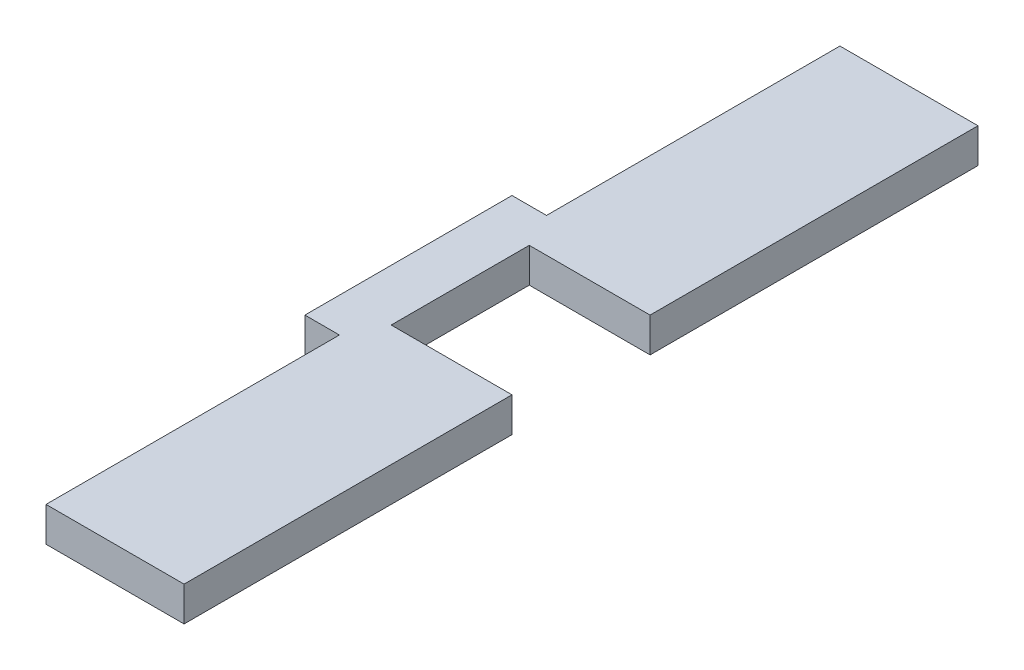
SolidWorks part; units mm, degrees
ref_plane "Front Plane" through (0, 0, 0) normal (0, 0, 1) x (1, 0, 0)
ref_plane "Top Plane" through (0, 0, 0) normal (0, 1, 0) x (1, 0, 0)
ref_plane "Right Plane" through (0, 0, 0) normal (1, 0, 0) x (0, 0, -1)
sketch "Sketch1" plane through (0, 0, 0) normal (0, 1, 0) x (1, 0, 0)
  line L0 (0, 36.5125) -> (-3.175, 36.5125) construction
  line L1 (0, 0) -> (12.7, 0)
  line L2 (0, 0) -> (0, 73.025)
  line L3 (0, 73.025) -> (12.7, 73.025)
  line L4 (12.7, 0) -> (12.7, 73.025)
  line L5 (0, 36.5125) -> (12.7, 36.5125) construction
  line L6 (0, 46.0375) -> (-3.175, 46.0375)
  line L7 (0, 46.0375) -> (0, 26.9875)
  line L8 (0, 26.9875) -> (-3.175, 26.9875)
  line L9 (-3.175, 46.0375) -> (-3.175, 26.9875)
  line L10 (0, 42.8625) -> (12.7, 42.8625)
  line L11 (0, 42.8625) -> (0, 30.1625)
  line L12 (0, 30.1625) -> (12.7, 30.1625)
  line L13 (12.7, 42.8625) -> (12.7, 30.1625)
  line L14 (1.5875, 42.8625) -> (1.5875, 30.1625)
  dimension "D1" = 73.025
  dimension "D2" = 12.7
  dimension "D3" = 3.175
  dimension "D4" = 19.05
  dimension "D5" = 12.7
  dimension "D6" = 1.5875
extrude "Boss-Extrude1" add sketch "Sketch1" along normal blind 3.175 contours L1 L4 L3 L2 L7 | L14 L10 L7 L12 | L12 L2 L1 L4
